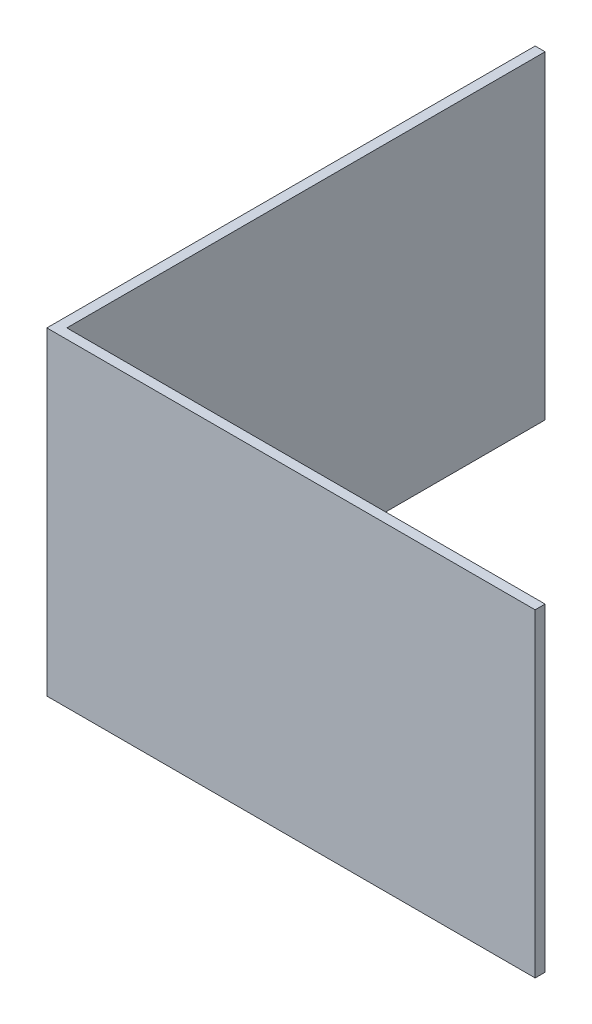
SolidWorks part; units mm, degrees
ref_plane "Front Plane" through (0, 0, 0) normal (0, 0, 1) x (1, 0, 0)
ref_plane "Top Plane" through (0, 0, 0) normal (0, 1, 0) x (1, 0, 0)
ref_plane "Right Plane" through (0, 0, 0) normal (1, 0, 0) x (0, 0, -1)
sketch "Sketch1" plane through (0, 0, 0) normal (0, 1, 0) x (1, 0, 0)
  line L0 (-37.3062, 38.8938) -> (38.8937, 38.8938) construction
  line L1 (-38.8937, -38.8938) -> (38.8938, -38.8938)
  line L2 (-38.8937, -38.8938) -> (-38.8937, 38.8938)
  line L3 (-38.8937, 38.8938) -> (-37.3062, 38.8938)
  line L4 (38.8938, -38.8938) -> (38.8937, -37.3062)
  line L5 (-38.8937, -38.8938) -> (38.8937, 38.8938) construction
  line L6 (-38.8937, 38.8938) -> (38.8938, -38.8938) construction
  line L9 (38.8937, -37.3062) -> (-37.3062, -37.3062)
  line L10 (-37.3062, 38.8938) -> (-37.3062, -37.3062)
  line L11 (38.8937, 38.8938) -> (38.8937, -37.3062) construction
  point P0 (0, 0)
  dimension "D1" = 76.2
  dimension "D2" = 1.5875
extrude "Boss-Extrude1" add sketch "Sketch1" along normal blind 50.8
